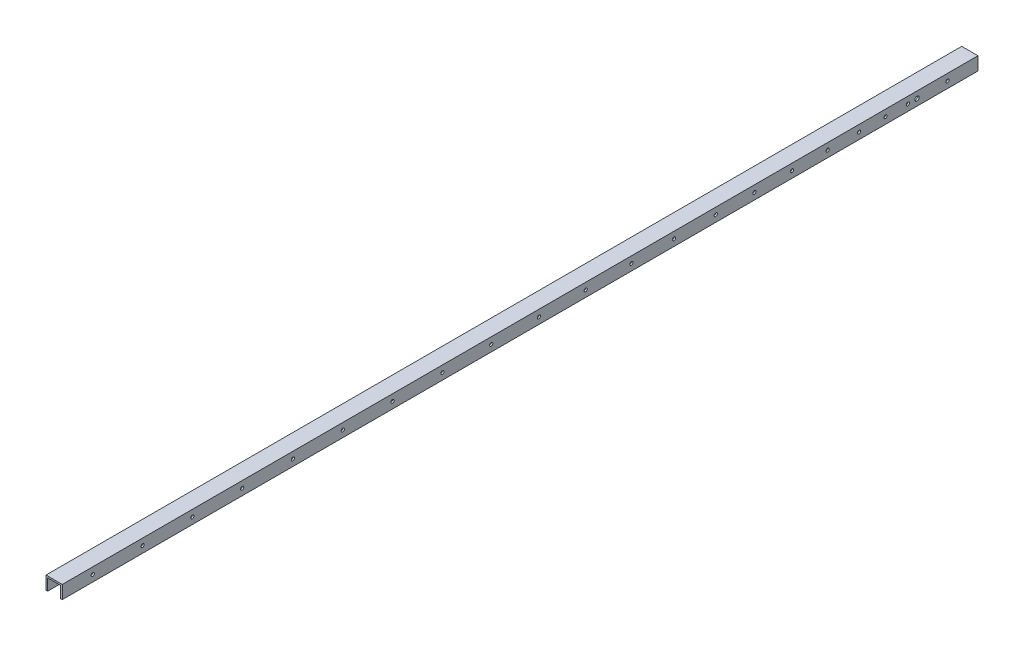
SolidWorks part; units mm, degrees
material "1060 Alloy"
ref_plane "Front Plane" through (0, 0, 0) normal (0, 0, 1) x (1, 0, 0)
ref_plane "Top Plane" through (0, 0, 0) normal (0, 1, 0) x (1, 0, 0)
ref_plane "Right Plane" through (0, 0, 0) normal (1, 0, 0) x (0, 0, -1)
sketch "Sketch1" plane through (0, 0, 0) normal (0, 0, 1) x (1, 0, 0)
  line L0 (-8, 6.5) -> (8, 6.5)
  line L5 (8, 6.5) -> (8, -6.5)
  line L6 (8, -6.5) -> (6.4, -6.5)
  line L11 (6.4, -6.5) -> (6.4, 4.9)
  line L12 (6.4, 4.9) -> (-6.4, 4.9)
  line L13 (-6.4, 4.9) -> (-6.4, -6.5)
  line L14 (-6.4, -6.5) -> (-8, -6.5)
  line L15 (-8, -6.5) -> (-8, 6.5)
  line L16 (-6.4, 4.9) -> (-6.4, 6.5) construction
  point P6 (0, 4.9)
  point P11 (-8, 0)
  dimension "D1" = 16
  dimension "D2" = 13
  dimension "D3" = 1.6
extrude "Boss-Extrude1" add sketch "Sketch1" along normal mid plane 901
sketch "Sketch2" plane through (8, 0, 0) normal (1, 0, 0) x (0, 0, -1)
  line L0 (420.5, -122.7932) -> (420.5, 153.1399) construction
  line L1 (450.5, -6.5) -> (450.5, 6.5) construction
  line L3 (-420.5, -34.9365) -> (-420.5, 27.8137) construction
  line L6 (-450.5, -6.5) -> (-450.5, 6.5) construction
  circle A0 centre (-371.5, 0) radius 1.5875
  circle A1 centre (-322.5, 0) radius 1.5875
  circle A2 centre (-273.5, 0) radius 1.5875
  circle A3 centre (-420.5, 0) radius 1.5875
  circle A4 centre (-223.5, 0) radius 1.5875
  circle A5 centre (-174.5, 0) radius 1.5875
  circle A6 centre (-125.5, 0) radius 1.5875
  circle A7 centre (-76.5, 0) radius 1.5875
  circle A8 centre (-28.5, 0) radius 1.5875
  circle A9 centre (18.5, 0) radius 1.5875
  circle A10 centre (64.5, 0) radius 1.5875
  circle A11 centre (109.5, 0) radius 1.5875
  circle A12 centre (151.5, 0) radius 1.5875
  circle A13 centre (192.5, 0) radius 1.5875
  circle A14 centre (230.5, 0) radius 1.5875
  circle A15 centre (267.5, 0) radius 1.5875
  circle A16 centre (302.5, 0) radius 1.5875
  circle A17 centre (333.5, 0) radius 1.5875
  circle A18 centre (359.5, 0) radius 1.5875
  circle A19 centre (381.5, 0) radius 1.5875
  circle A20 centre (420.5, 0) radius 1.5875
  circle A21 centre (390.5, 0) radius 2.1
  dimension "D2" = 61
  dimension "D4" = 118
  dimension "D5" = 153
  dimension "D7" = 228
  dimension "D12" = 449
  dimension "D13" = 497
  dimension "D21" = 30
  dimension "D22" = 3.175
  dimension "D23" = 30
  dimension "D25" = 4.2
  dimension "D1" = 39
  dimension "D3" = 87
  dimension "D6" = 190
  dimension "D8" = 269
  dimension "D9" = 311
  dimension "D10" = 356
  dimension "D11" = 402
  dimension "D14" = 546
  dimension "D15" = 595
  dimension "D16" = 644
  dimension "D17" = 694
  dimension "D18" = 743
  dimension "D19" = 792
  dimension "D20" = 841
  dimension "D24" = 30
extrude "Cut-Extrude1" cut sketch "Sketch2" against normal through all
